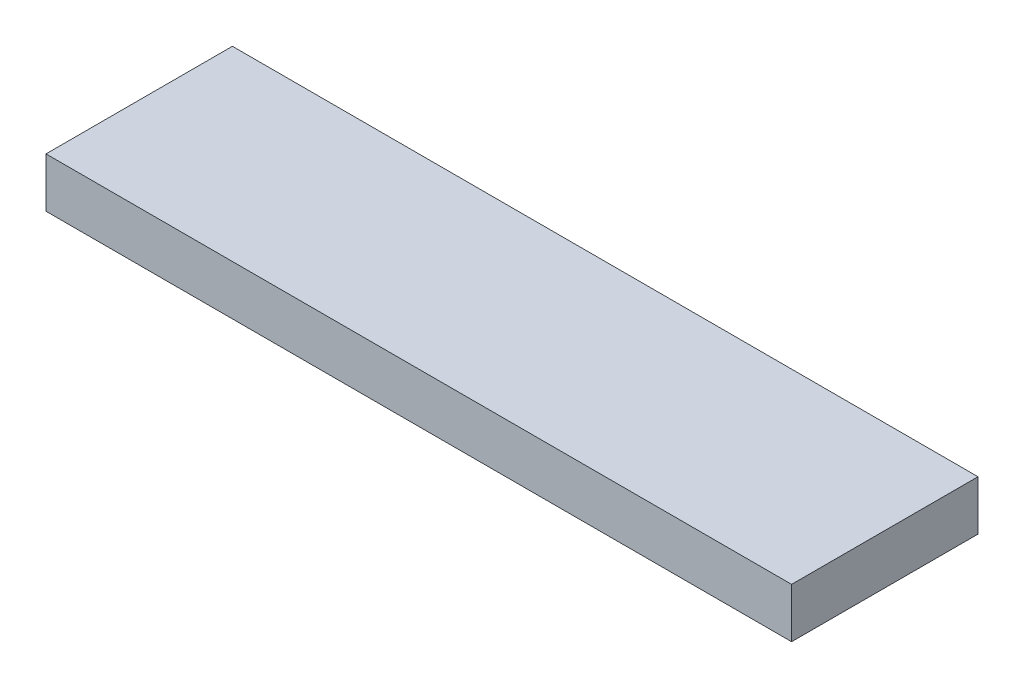
SolidWorks part; units mm, degrees
ref_plane "Front Plane" through (0, 0, 0) normal (0, 0, 1) x (1, 0, 0)
ref_plane "Top Plane" through (0, 0, 0) normal (0, 1, 0) x (1, 0, 0)
ref_plane "Right Plane" through (0, 0, 0) normal (1, 0, 0) x (0, 0, -1)
sketch "Sketch1" plane through (0, 0, 0) normal (0, 1, 0) x (1, 0, 0)
  line L1 (38.1, 9.525) -> (-38.1, 9.525)
  line L2 (38.1, 9.525) -> (38.1, -9.525)
  line L3 (38.1, -9.525) -> (-38.1, -9.525)
  line L4 (-38.1, 9.525) -> (-38.1, -9.525)
  line L5 (38.1, 9.525) -> (-38.1, -9.525) construction
  line L6 (38.1, -9.525) -> (-38.1, 9.525) construction
  point P0 (0, 0)
  dimension "D1" = 76.2
  dimension "D2" = 19.05
extrude "Boss-Extrude1" add sketch "Sketch1" along normal blind 5.08
